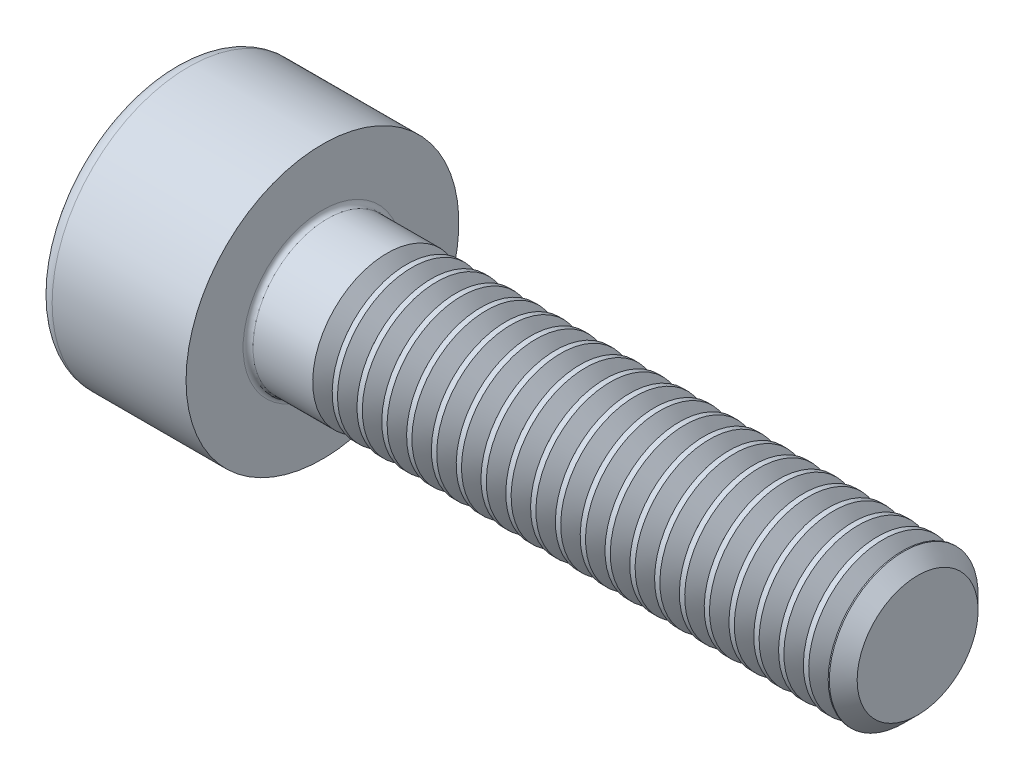
SolidWorks part; units mm, degrees
revolve "Base-Revolve" add sketch "BodySke"
sketch "BodySke" plane through (0, 0, 0) normal (0, 0, 1) x (1, 0, 0)
  line L0 (0, 0) -> (0, 2.75)
  line L1 (0, 2.75) -> (3, 2.75)
  line L2 (3, 2.75) -> (3, 1.5)
  line L3 (3, 1.5) -> (14.7195, 1.5)
  line L4 (15, 1.2195) -> (15, 0)
  line L5 (15, 0) -> (0, 0)
  line L6 (-31.75, 0) -> (127, 0) construction
  line L8 (15, 1.2195) -> (14.7195, 1.5)
  line L10 (15, -1.2195) -> (14.7195, -1.5) construction
  line L11 (3.5, 9.525) -> (3.5, 3.175) construction
  line L12 (3, 9.525) -> (3, 3.175) construction
  line L13 (3, 9.525) -> (3, 3.175) construction
cosmetic thread "ThreadCosmetic" [suppressed]
fillet "Fillet1" radius 0.1 1 edges at (3, 0, 1.5)
fillet "Fillet2" radius 0.3 1 edges at (0, 0, 2.75)
ref_plane "Plane1" through (0, 0, 0) normal (0, 0, 1) x (1, 0, 0)
ref_plane "Plane2" through (0, 0, 0) normal (0, 1, 0) x (1, 0, 0)
ref_plane "Plane3" through (0, 0, 0) normal (1, 0, 0) x (0, 0, -1)
sketch "Sketch2" plane through (0, 0, 0) normal (0, 0, 1) x (1, 0, 0)
  line L0 (0, 1.26) -> (1.3, 1.26)
  line L1 (1.3, 1.26) -> (2.0275, 0)
  line L2 (-31.75, 0) -> (127, 0) construction
  line L3 (2.0275, 0) -> (0, 0)
  line L4 (0, 0) -> (0, 1.26)
  line L6 (0, 0) -> (47.625, 0) construction
revolve "Hex-PreBroach" cut sketch "Sketch2" angle 360 about L6
sketch "Sketch3" plane through (0, 0, 0) normal (-1, 0, 0) x (0, 0.5, 0.866)
  line L0 (0.7275, 1.26) -> (-0.7275, 1.26)
  line L1 (-0.7275, 1.26) -> (-1.4549, 0)
  line L2 (0.7275, 1.26) -> (1.4549, 0)
  line L3 (0.7275, -1.26) -> (1.4549, 0)
  line L4 (0.7275, -1.26) -> (-0.7275, -1.26)
  line L5 (-0.7275, -1.26) -> (-1.4549, 0)
extrude "Hex" cut sketch "Sketch3" against normal blind 1.3
sketch "ThdSchSke" plane through (0, 0, 0) normal (0, 0, 1) x (1, 0, 0)
  line L0 (4.5, -1.2195) -> (4.3036, -1.5)
  line L1 (4.5, -1.2195) -> (4.6964, -1.5)
  line L2 (4.6964, -1.5) -> (4.6964, -1.875)
  line L3 (-3.175, 0) -> (5.1513, 0) construction
  line L4 (0, 2.45) -> (0, -2.45) construction
  line L5 (4.6964, -1.875) -> (4.3036, -1.875)
  line L6 (4.3036, -1.875) -> (4.3036, -1.5)
revolve "ThreadSchematic" cut sketch "ThdSchSke" angle 360 about L3
pattern_linear "ThdSchPat" count 21 spacing 0.5 along (1, 0, 0) of "ThreadSchematic"
equation "\"D2@Sketch3\" = \"Hex_size@Sketch3\" / 2"
equation "\"D1@Sketch3\" = \"Hex_size@Sketch3\" / 2"
equation "\"D1@Sketch2\" = \"Hex_size@Sketch3\" / 2"
equation "\"Thread_minor@ThreadCosmetic\"  =  \"Minor_dia@BodySke\""
equation "\"Depth@Sketch2\" =  \"Key_eng@Hex\""
equation "\"Thread_length@ThreadCosmetic\" = ((sgn( (\"Length@BodySke\" - \"Advance@BodySke\" * 3.0) - \"Thread_nom@BodySke\" )-1)*( (\"Length@BodySke\" - \"Advance@BodySke\" * 3.0) - \"Thread_nom@BodySke\" ))/-2+ \"Thread_nom@BodySke\""
equation "\"Thread_minor@ThdSchSke\" = \"Minor_dia@BodySke\""
equation "\"Diameter@ThdSchSke\" = \"Diameter@BodySke\""
equation "\"Overcut@ThdSchSke\" = \"Diameter@BodySke\" * 1.25"
equation "\"Start@ThdSchSke\" = \"Head_ht@BodySke\" + \"Length@BodySke\" - \"Thread_length@ThreadCosmetic\"  '---Non-countersunk---"
equation "\"Num_threads@ThdSchPat\" = int( \"Thread_length@ThreadCosmetic\" / \"Advance@BodySke\" + 0.999 )  + 1"
equation "\"Advance@ThdSchPat\" = \"Thread_length@ThreadCosmetic\" /  (\"Num_threads@ThdSchPat\" - 1) 'relax it"
equation "\"Num_threads@ThdSchPat\" = \"Num_threads@ThdSchPat\" - sgn( \"Num_threads@ThdSchPat\" - 1) '---chamfered tips only---"
